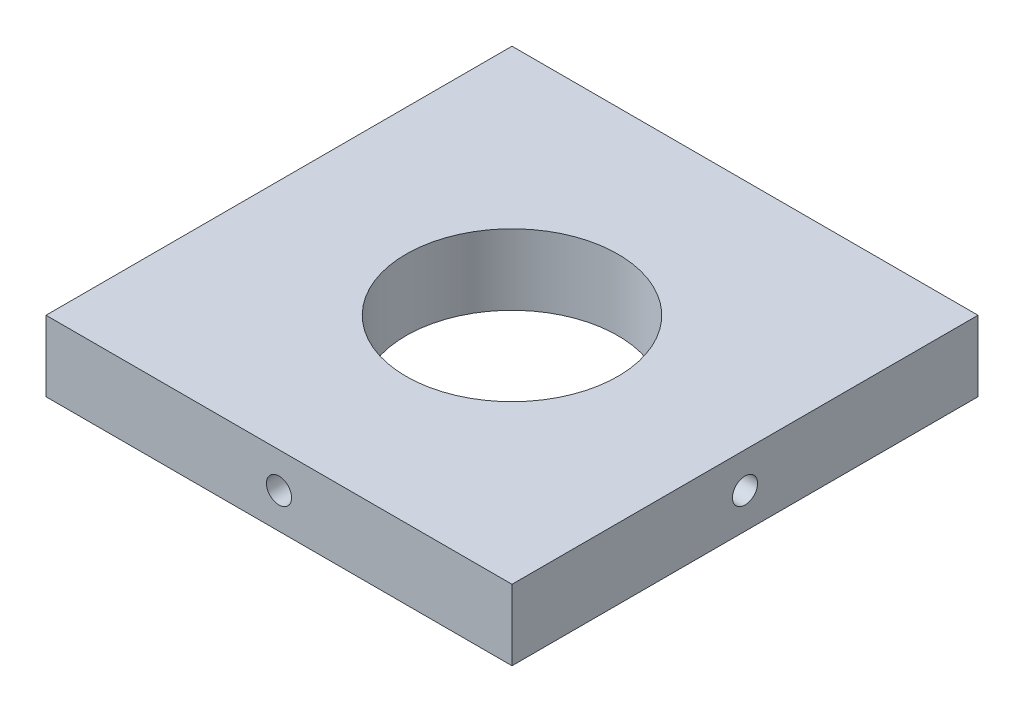
SolidWorks part; units mm, degrees
ref_plane "Front Plane" through (0, 0, 0) normal (0, 0, 1) x (1, 0, 0)
ref_plane "Top Plane" through (0, 0, 0) normal (0, 1, 0) x (1, 0, 0)
ref_plane "Right Plane" through (0, 0, 0) normal (1, 0, 0) x (0, 0, -1)
sketch "Sketch1" plane through (0, 0, 0) normal (0, 1, 0) x (1, 0, 0)
  line L1 (-16.5, -16.5) -> (16.5, -16.5)
  line L2 (-16.5, -16.5) -> (-16.5, 16.5)
  line L3 (-16.5, 16.5) -> (16.5, 16.5)
  line L4 (16.5, -16.5) -> (16.5, 16.5)
  circle A0 centre (0, 0) radius 7.5
extrude "Boss-Extrude1" add sketch "Sketch1" along normal blind 5
sketch "Sketch2" plane through (0, 0, 16.5) normal (0, 0, 1) x (1, 0, 0)
  line L0 (-16.5, 5) -> (16.5, 0)
  line L1 (-16.5, 0) -> (16.5, 5)
hole_wizard "#2-56 Tapped Hole4" positions "Sketch14" profile "Sketch15" tap size "#2-56" standard "ANSI Inch"
sketch "Sketch14" plane through (0, 0, 16.5) normal (0, 0, 1) x (1, 0, 0)
  line L0 (-16.5, 5) -> (16.5, 0) construction
  point P0 (0, 2.5)
sketch "Sketch15" plane through (0, 2.5, 16.5) normal (1, 0, 0) x (0, -1, 0)
  line L0 (0, 0) -> (0, 8)
  line L1 (0, 8) -> (0.889, 7.4658)
  line L2 (0.889, 7.4658) -> (0.889, 0)
  line L5 (0.889, 0) -> (0, 0)
  line L10 (0, 8) -> (-0.889, 7.4658) construction
  line L11 (0, -6.35) -> (0, 107.95) construction
  dimension "Tap Drill Dia." = 1.778
  dimension "Tap Drill Depth" = 8
  dimension "Drill Angle" = 118
cosmetic thread "Hole Thread4"
sketch "Sketch18" plane through (0, 0, -16.5) normal (0, 0, -1) x (-1, 0, 0)
  line L0 (-16.5, 5) -> (16.5, 0)
  line L1 (-16.5, 0) -> (16.5, 5)
hole_wizard "#2-56 Tapped Hole5" positions "Sketch19" profile "Sketch20" tap size "#2-56" standard "ANSI Inch"
sketch "Sketch19" plane through (0, 0, -16.5) normal (0, 0, -1) x (-1, 0, 0)
  line L0 (16.5, 5) -> (-16.5, 0) construction
  point P0 (0, 2.5)
sketch "Sketch20" plane through (0, 2.5, -16.5) normal (1, 0, 0) x (0, 1, 0)
  line L0 (0, 0) -> (0, 8)
  line L1 (0, 8) -> (0.889, 7.4658)
  line L2 (0.889, 7.4658) -> (0.889, 0)
  line L5 (0.889, 0) -> (0, 0)
  line L10 (0, 8) -> (-0.889, 7.4658) construction
  line L11 (0, -6.35) -> (0, 107.95) construction
  dimension "Tap Drill Dia." = 1.778
  dimension "Tap Drill Depth" = 8
  dimension "Drill Angle" = 118
cosmetic thread "Hole Thread5"
sketch "Sketch21" plane through (16.5, 0, 0) normal (1, 0, 0) x (0, 0, -1)
  line L0 (-16.5, 5) -> (16.5, 0)
  line L1 (16.5, 5) -> (-16.5, 0)
  line L2 (-16.5, 0) -> (-16.5, 5) construction
  line L3 (-16.5, 0) -> (16.5, 0) construction
hole_wizard "#2-56 Tapped Hole6" positions "Sketch22" profile "Sketch23" tap size "#2-56" standard "ANSI Inch"
sketch "Sketch22" plane through (16.5, 0, 0) normal (1, 0, 0) x (0, 0, -1)
  line L0 (-16.5, 5) -> (16.5, 0) construction
  point P0 (0, 2.5)
sketch "Sketch23" plane through (16.5, 2.5, 0) normal (0, 1, 0) x (0, 0, -1)
  line L0 (0, 0) -> (0, 8)
  line L1 (0, 8) -> (0.889, 7.4658)
  line L2 (0.889, 7.4658) -> (0.889, 0)
  line L5 (0.889, 0) -> (0, 0)
  line L10 (0, 8) -> (-0.889, 7.4658) construction
  line L11 (0, -6.35) -> (0, 107.95) construction
  dimension "Tap Drill Dia." = 1.778
  dimension "Tap Drill Depth" = 8
  dimension "Drill Angle" = 118
cosmetic thread "Hole Thread6"
sketch "Sketch24" plane through (-16.5, 0, 0) normal (-1, 0, 0) x (0, 0, 1)
  line L0 (-16.5, 5) -> (16.5, 0)
  line L1 (-16.5, 0) -> (16.5, 5)
hole_wizard "#2-56 Tapped Hole7" positions "Sketch25" profile "Sketch26" tap size "#2-56" standard "ANSI Inch"
sketch "Sketch25" plane through (-16.5, 0, 0) normal (-1, 0, 0) x (0, 0, 1)
  line L0 (16.5, 5) -> (-16.5, 0) construction
  point P0 (0, 2.5)
sketch "Sketch26" plane through (-16.5, 2.5, 0) normal (0, 1, 0) x (0, 0, 1)
  line L0 (0, 0) -> (0, 8)
  line L1 (0, 8) -> (0.889, 7.4658)
  line L2 (0.889, 7.4658) -> (0.889, 0)
  line L5 (0.889, 0) -> (0, 0)
  line L10 (0, 8) -> (-0.889, 7.4658) construction
  line L11 (0, -6.35) -> (0, 107.95) construction
  dimension "Tap Drill Dia." = 1.778
  dimension "Tap Drill Depth" = 8
  dimension "Drill Angle" = 118
cosmetic thread "Hole Thread7" parameters "D1"=8, "D2"=2.1844
